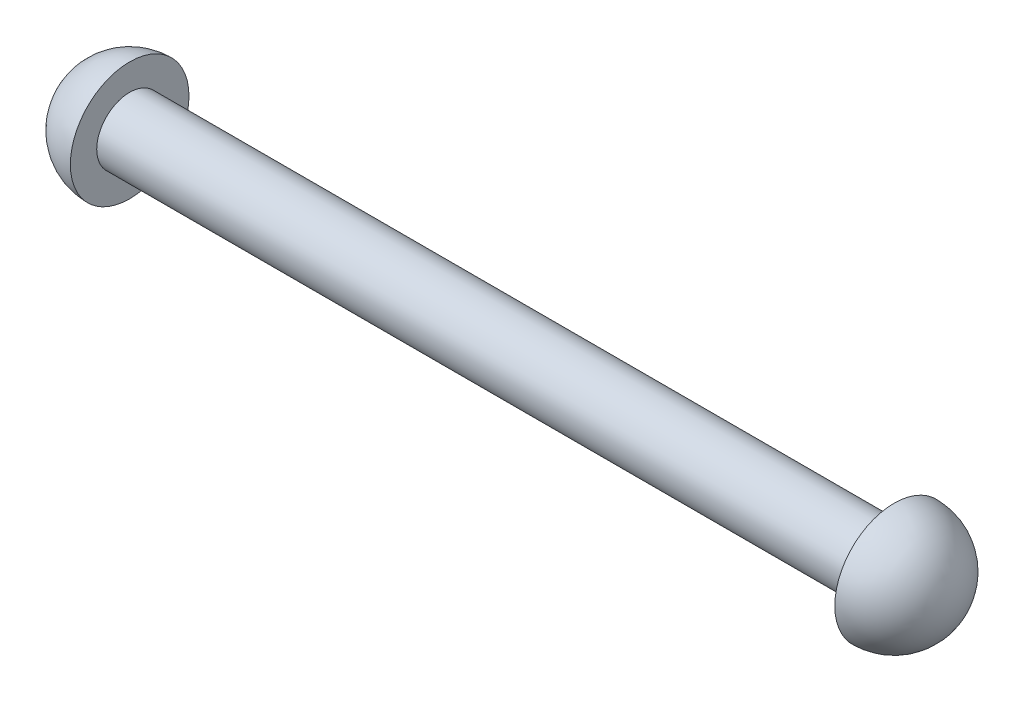
SolidWorks part; units mm, degrees
material "AISI 1020"
ref_plane "Front Plane" through (0, 0, 0) normal (0, 0, 1) x (1, 0, 0)
ref_plane "Top Plane" through (0, 0, 0) normal (0, 1, 0) x (1, 0, 0)
ref_plane "Right Plane" through (0, 0, 0) normal (1, 0, 0) x (0, 0, -1)
sketch "Sketch1" plane through (0, 0, 0) normal (0, 1, 0) x (1, 0, 0)
  line L15 (-36.83, -3.175) -> (36.83, -3.175)
  line L20 (36.83, -3.175) -> (36.83, -5.715)
  line L25 (-36.83, -3.175) -> (-36.83, -5.715)
  line L26 (-36.83, 0) -> (42.545, 0)
  line L27 (42.545, 0) -> (-42.545, 0)
  arc A7 (42.545, 0) -> (36.83, -5.715) centre (36.83, 0) cw
  arc A8 (-42.545, 0) -> (-36.83, -5.715) centre (-36.83, 0) ccw
  point P0 (0, 0)
  point P9 (-36.83, 0)
revolve "Revolve9" add sketch "Sketch1" angle 360 about L26
